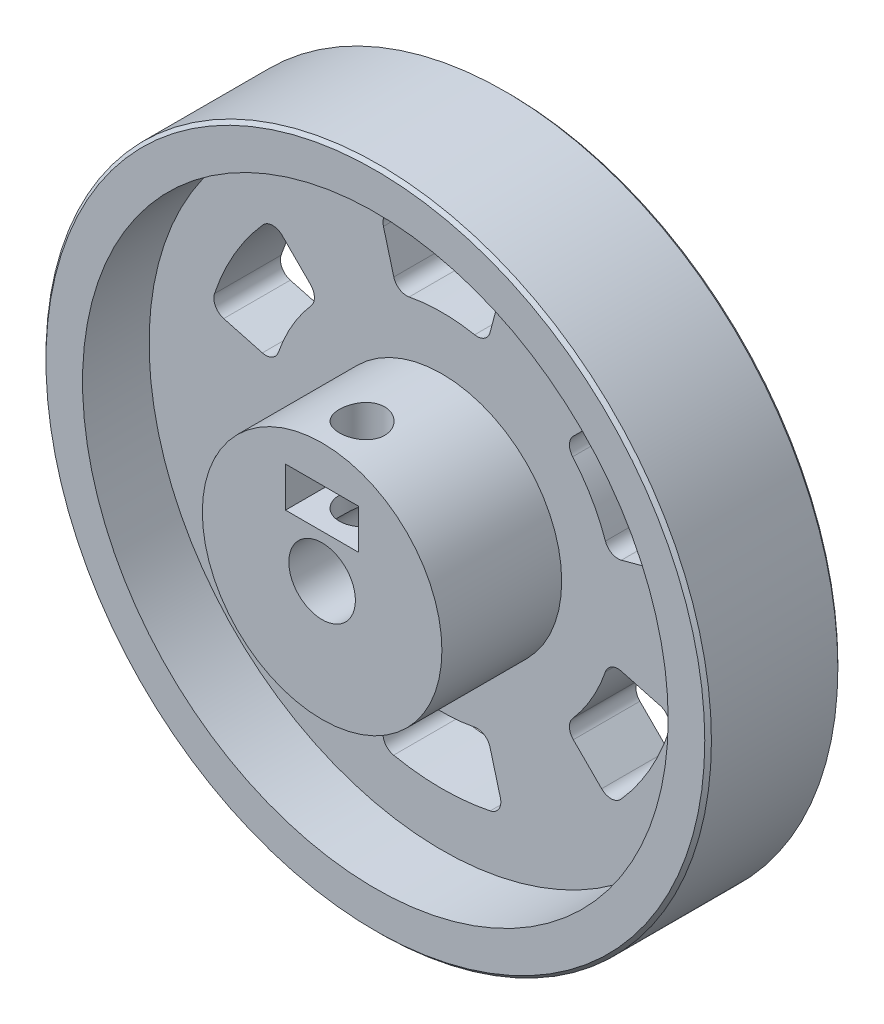
SolidWorks part; units mm, degrees
material "ABS"
ref_plane "Front Plane" through (0, 0, 0) normal (0, 0, 1) x (1, 0, 0)
ref_plane "Top Plane" through (0, 0, 0) normal (0, 1, 0) x (1, 0, 0)
ref_plane "Right Plane" through (0, 0, 0) normal (1, 0, 0) x (0, 0, -1)
sketch "Sketch1" plane through (0, 0, 0) normal (0, 0, 1) x (1, 0, 0)
  circle A0 centre (0, 0) radius 25
  dimension "D1" = 50
extrude "Boss-Extrude1" add sketch "Sketch1" along normal blind 5
sketch "Sketch3" plane through (0, 0, 0) normal (0, 0, 1) x (1, 0, 0)
  circle A0 centre (0, 0) radius 22
  circle A1 centre (0, 0) radius 25 construction
  circle A2 centre (0, 0) radius 25
  dimension "D1" = 3
extrude "Boss-Extrude3" add sketch "Sketch3" along normal blind 10
sketch "Sketch4" plane through (0, 0, 0) normal (0, 0, 1) x (1, 0, 0)
  circle A0 centre (0, 0) radius 9
  dimension "D1" = 18
extrude "Boss-Extrude4" add sketch "Sketch4" along normal blind 14
sketch "Sketch5" plane through (0, 0, 0) normal (0, 0, 1) x (1, 0, 0)
  circle A0 centre (0, 0) radius 2.5
  dimension "D1" = 5
extrude "Cut-Extrude1" cut sketch "Sketch5" along normal through all
sketch "Sketch6" plane through (0, 0, 14) normal (0, 0, 1) x (1, 0, 0)
  line L0 (0, 4.75) -> (0, 0) construction
  line L1 (-2.75, 6.25) -> (2.75, 6.25)
  line L2 (-2.75, 6.25) -> (-2.75, 3.25)
  line L3 (-2.75, 3.25) -> (2.75, 3.25)
  line L4 (2.75, 6.25) -> (2.75, 3.25)
  line L5 (-2.75, 6.25) -> (2.75, 3.25) construction
  line L6 (-2.75, 3.25) -> (2.75, 6.25) construction
  point P0 (0, 4.75)
  dimension "D1" = 3
  dimension "D2" = 5.5
  dimension "D3" = 4.75
extrude "Cut-Extrude2" cut sketch "Sketch6" against normal blind 6
sketch "Sketch7" plane through (0, 0, 0) normal (0, 1, 0) x (1, 0, 0)
  line L0 (0, 0) -> (0, -11) construction
  line L1 (2.75, -14) -> (-2.75, -14) construction
  circle A0 centre (0, -11) radius 1.7
  point P3 (0, -14)
  dimension "D2" = 3.4
  dimension "D1" = 3
extrude "Cut-Extrude3" cut sketch "Sketch7" along normal up to surface (9 mm away)
sketch "Sketch8" plane through (0, 0, 0) normal (0, 0, 1) x (1, 0, 0)
  line L0 (0, 22) -> (0, 9) construction
  line L1 (0, 0) -> (-5.694, 21.2504) construction
  line L2 (-4.3923, 16.3923) -> (-3.6142, 13.4884)
  line L3 (0, 18) -> (0, 13) construction
  line L4 (4.3923, 16.3923) -> (3.6142, 13.4884)
  arc A0 (-3.6279, 17.6306) -> (3.6279, 17.6306) centre (0, 0) cw
  circle A1 centre (0, 0) radius 22 construction
  circle A2 centre (0, 0) radius 22 construction
  circle A3 centre (0, 0) radius 9 construction
  arc A4 (-2.4591, 12.7653) -> (2.4591, 12.7653) centre (0, 0) cw
  arc A5 (-2.4591, 12.7653) -> (-3.6142, 13.4884) centre (-2.6483, 13.7472) cw
  arc A6 (-3.6279, 17.6306) -> (-4.3923, 16.3923) centre (-3.4264, 16.6511) ccw
  arc A7 (2.4591, 12.7653) -> (3.6142, 13.4884) centre (2.6483, 13.7472) ccw
  arc A8 (3.6279, 17.6306) -> (4.3923, 16.3923) centre (3.4264, 16.6511) cw
  point P11 (0, 15.5)
  point P19 (-3.3646, 12.557)
  point P22 (-4.6587, 17.3867)
  point P23 (0, 15.5)
  dimension "D1" = 1
  dimension "D2" = 4
  dimension "D3" = 15
extrude "Cut-Extrude4" cut sketch "Sketch8" along normal through all
pattern_circular "CirPattern1" count 6 over 360 about axis through (0, 0, 0) along (0, 0, 1) of "Cut-Extrude4"
chamfer "Chamfer1" distance 0.25 angle 45 2 edges at (25, 0, 10) (25, 0, 0)
ref_plane "Plane1" through (0, 0, 5) normal (0, 0, 1) x (1, 0, 0)
